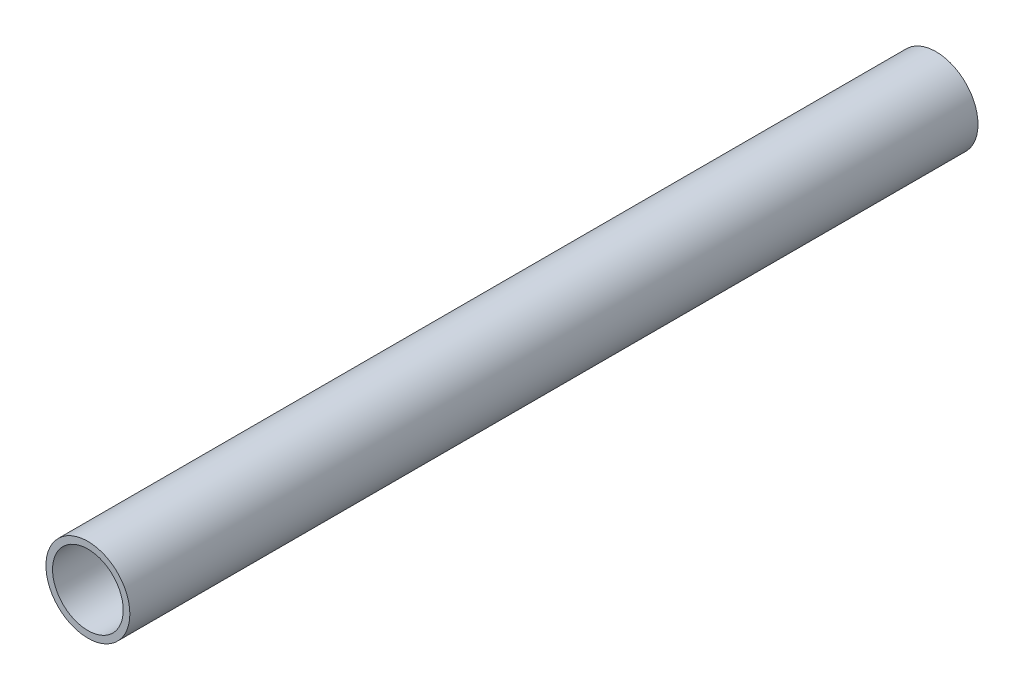
SolidWorks part; units mm, degrees
ref_plane "Front Plane" through (0, 0, 0) normal (0, 0, 1) x (1, 0, 0)
ref_plane "Top Plane" through (0, 0, 0) normal (0, 1, 0) x (1, 0, 0)
ref_plane "Right Plane" through (0, 0, 0) normal (1, 0, 0) x (0, 0, -1)
sketch "Sketch1" plane through (0, 0, 0) normal (0, 0, 1) x (1, 0, 0)
  circle A0 centre (0, 0) radius 30.1625
  circle A1 centre (0, 0) radius 25.4
  dimension "D1" = 50.8
  dimension "D2" = 60.325
extrude "Boss-Extrude1" add sketch "Sketch1" along normal mid plane 609.6
